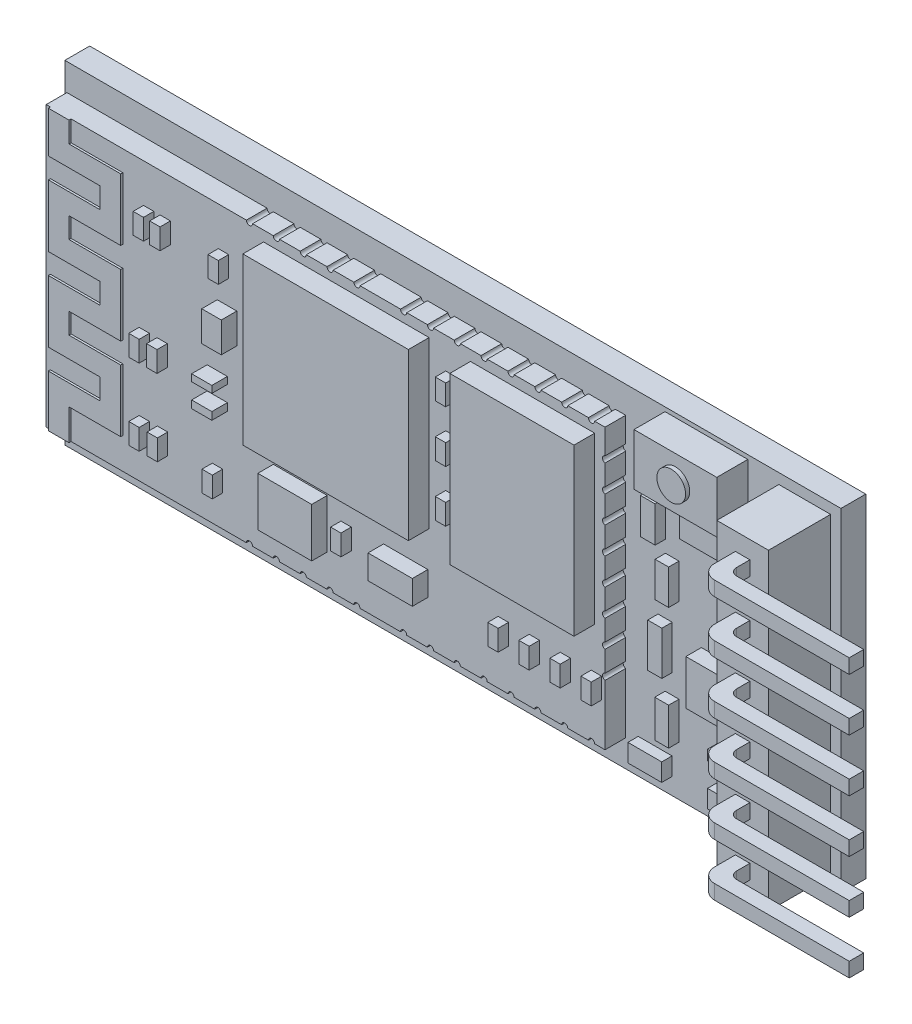
SolidWorks part; units mm, degrees
ref_plane "Ön Düzlem" through (0, 0, 0) normal (0, 0, 1) x (1, 0, 0)
ref_plane "Üst Düzlem" through (0, 0, 0) normal (0, 1, 0) x (1, 0, 0)
ref_plane "Sağ Düzlem" through (0, 0, 0) normal (1, 0, 0) x (0, 0, -1)
sketch "Çizim2" plane through (0, 0, 0) normal (0, 0, 1) x (1, 0, 0)
  line L1 (0, 0) -> (37.5, 0)
  line L2 (0, 0) -> (0, 16.1)
  line L3 (0, 16.1) -> (37.5, 16.1)
  line L4 (37.5, 0) -> (37.5, 16.1)
  dimension "D1" = 37.5
  dimension "D2" = 16.1
extrude "Yükseklik-Ekstrüzyon1" add sketch "Çizim2" along normal blind 1.2
sketch "Çizim5" plane through (0, 0, 1.2) normal (0, 0, 1) x (1, 0, 0)
  line L0 (37.5, 0) -> (37.5, 16.1) construction
  line L1 (34.5, 0.5) -> (37, 0.5)
  line L2 (34.5, 0.5) -> (34.5, 15.6)
  line L3 (34.5, 15.6) -> (37, 15.6)
  line L4 (37, 0.5) -> (37, 15.6)
  line L5 (0, 0) -> (37.5, 0) construction
  line L6 (37.5, 16.1) -> (0, 16.1) construction
  dimension "D1" = 0.5
  dimension "D2" = 0.5
  dimension "D3" = 0.5
  dimension "D4" = 2.5
extrude "Yükseklik-Ekstrüzyon2" add sketch "Çizim5" along normal blind 3
sketch "Çizim14" plane through (0, 0, 1.2) normal (0, 0, 1) x (1, 0, 0)
  line L1 (0.1, 14.8) -> (27.1, 14.8)
  line L2 (0.1, 14.8) -> (0.1, 1.3)
  line L3 (0.1, 1.3) -> (27.1, 1.3)
  line L4 (27.1, 14.8) -> (27.1, 1.3)
  line L5 (37.5, 16.1) -> (0, 16.1) construction
  line L7 (0, 16.1) -> (0, 0) construction
  point P6 (0, 8.05)
  dimension "D1" = 13.5
  dimension "D2" = 27
  dimension "D3" = 1.3
  dimension "D4" = 0.1
extrude "Yükseklik-Ekstrüzyon10" add sketch "Çizim14" along normal blind 1
sketch "Çizim15" plane through (0, 0, 2.2) normal (0, 0, 1) x (1, 0, 0)
  line L0 (0.3, 1.3) -> (0.3, 14.8) construction
  line L1 (0.1, 1.3) -> (27.1, 1.3) construction
  line L2 (27.1, 14.8) -> (0.1, 14.8) construction
  line L3 (0.1, 14.8) -> (0.1, 1.3) construction
  line L4 (3.8, 14.8) -> (3.8, 1.3) construction
  line L5 (0.3, 1.3) -> (0.3, 3.8)
  line L6 (1.3, 2.8) -> (3.8, 2.8)
  line L7 (3.8, 2.8) -> (3.8, 5.8)
  line L8 (0.3, 3.8) -> (2.8, 3.8)
  line L9 (1.3, 1.3) -> (1.3, 2.8)
  line L10 (0.1, 1.3) -> (27.1, 1.3) construction
  line L11 (2.8, 3.8) -> (2.8, 4.8)
  line L12 (2.8, 4.8) -> (0.3, 4.8)
  line L13 (0.3, 4.8) -> (0.3, 7.8)
  line L14 (0.3, 7.8) -> (2.8, 7.8)
  line L15 (3.8, 5.8) -> (1.3, 5.8)
  line L16 (1.3, 5.8) -> (1.3, 6.8)
  line L17 (1.3, 6.8) -> (3.8, 6.8)
  line L18 (3.8, 6.8) -> (3.8, 9.8)
  line L19 (2.8, 7.8) -> (2.8, 8.8)
  line L20 (2.8, 8.8) -> (0.3, 8.8)
  line L21 (0.3, 8.8) -> (0.3, 11.8)
  line L22 (3.8, 9.8) -> (1.3, 9.8)
  line L23 (1.3, 9.8) -> (1.3, 10.8)
  line L24 (1.3, 10.8) -> (3.8, 10.8)
  line L25 (3.8, 10.8) -> (3.8, 13.8)
  line L26 (0.3, 11.8) -> (2.8, 11.8)
  line L27 (2.8, 11.8) -> (2.8, 12.8)
  line L28 (2.8, 12.8) -> (0.3, 12.8)
  line L29 (0.3, 12.8) -> (0.3, 14.8)
  line L30 (3.8, 13.8) -> (1.3, 13.8)
  line L31 (1.3, 13.8) -> (1.3, 14.8)
  line L32 (1.3, 14.8) -> (0.3, 14.8)
  line L33 (1.3, 1.3) -> (0.3, 1.3)
  dimension "D1" = 0.2
  dimension "D2" = 3.5
  dimension "D3" = 2.5
  dimension "D4" = 1
  dimension "D5" = 1.5
  dimension "D6" = 3
  dimension "D7" = 1
  dimension "D8" = 1
  dimension "D9" = 1
  dimension "D10" = 1
  dimension "D11" = 1
  dimension "D12" = 2.5
  dimension "D13" = 3
  dimension "D14" = 2.5
  dimension "D15" = 3
  dimension "D16" = 1
  dimension "D17" = 1
  dimension "D18" = 1
  dimension "D19" = 2.5
  dimension "D20" = 2.5
  dimension "D21" = 1
  dimension "D22" = 3
  dimension "D23" = 1
extrude "Yükseklik-Ekstrüzyon11" add sketch "Çizim15" along normal blind 0.1
sketch "Çizim16" plane through (0, 0, 1.2) normal (0, 0, 1) x (1, 0, 0)
  line L0 (37.5, 16.1) -> (0, 16.1) construction
  line L1 (29, 15.9) -> (33, 15.9)
  line L2 (29, 15.9) -> (29, 13.4)
  line L3 (29, 13.4) -> (33, 13.4)
  line L4 (33, 15.9) -> (33, 13.4)
  line L5 (34.5, 15.6) -> (34.5, 0.5) construction
  dimension "D1" = 2.5
  dimension "D2" = 4
  dimension "D3" = 0.2
  dimension "D4" = 1.5
extrude "Yükseklik-Ekstrüzyon12" add sketch "Çizim16" along normal blind 1.5 separate body
sketch "Çizim17" plane through (0, 0, 2.7) normal (0, 0, 1) x (1, 0, 0)
  line L0 (29, 14.65) -> (33, 14.65) construction
  line L1 (29, 15.9) -> (29, 13.4) construction
  line L2 (33, 13.4) -> (33, 15.9) construction
  line L3 (31, 15.9) -> (31, 13.4) construction
  line L4 (33, 15.9) -> (29, 15.9) construction
  line L5 (29, 13.4) -> (33, 13.4) construction
  circle A0 centre (31, 14.65) radius 0.6936
extrude "Yükseklik-Ekstrüzyon13" add sketch "Çizim17" along normal blind 0.2
sketch "Çizim18" plane through (0, 0, 2.2) normal (0, 0, 1) x (1, 0, 0)
  line L0 (27.1, 14.8) -> (1.3, 14.8) construction
  line L1 (26.6004, 6.3) -> (20.6004, 6.3)
  line L2 (26.6004, 6.3) -> (26.6004, 14.3)
  line L3 (26.6004, 14.3) -> (20.6004, 14.3)
  line L4 (20.6004, 6.3) -> (20.6004, 14.3)
  line L5 (27.1, 1.3) -> (27.1, 14.8) construction
  line L7 (18.6004, 6.3) -> (10.6004, 6.3)
  line L8 (18.6004, 6.3) -> (18.6004, 14.3)
  line L9 (18.6004, 14.3) -> (10.6004, 14.3)
  line L10 (10.6004, 6.3) -> (10.6004, 14.3)
  dimension "D1" = 8
  dimension "D2" = 6
  dimension "D3" = 0.5
  dimension "D4" = 0.4996
  dimension "D5" = 2
  dimension "D6" = 8
  dimension "D7" = 8
  dimension "D8" = 0.5
extrude "Yükseklik-Ekstrüzyon14" add sketch "Çizim18" along normal blind 1
sketch "Çizim19" plane through (0, 0, 2.2) normal (0, 0, 1) x (1, 0, 0)
  line L0 (3.8, 10.8) -> (3.8, 13.8) construction
  line L1 (4.8, 11.93) -> (5.3, 11.93)
  line L2 (4.8, 11.93) -> (4.8, 12.93)
  line L3 (4.8, 12.93) -> (5.3, 12.93)
  line L4 (5.3, 11.93) -> (5.3, 12.93)
  line L5 (5.6, 11.93) -> (6.1, 11.93)
  line L6 (5.6, 11.93) -> (5.6, 12.93)
  line L7 (5.6, 12.93) -> (6.1, 12.93)
  line L8 (6.1, 11.93) -> (6.1, 12.93)
  line L9 (8.4157, 11.93) -> (8.9157, 11.93)
  line L10 (8.4157, 11.93) -> (8.4157, 12.93)
  line L11 (8.4157, 12.93) -> (8.9157, 12.93)
  line L12 (8.9157, 11.93) -> (8.9157, 12.93)
  dimension "D1" = 1
  dimension "D2" = 0.5
  dimension "D3" = 1
  dimension "D4" = 0.5
  dimension "D5" = 1
  dimension "D6" = 0.5
  dimension "D7" = 1
  dimension "D8" = 0.3
extrude "Yükseklik-Ekstrüzyon15" add sketch "Çizim19" along normal blind 0.5
sketch "Çizim22" plane through (0, 0, 2.2) normal (0, 0, 1) x (1, 0, 0)
  line L0 (4.589, 6.722) -> (5.089, 6.722)
  line L1 (4.589, 6.722) -> (4.589, 7.722)
  line L2 (4.589, 7.722) -> (5.089, 7.722)
  line L3 (5.089, 6.722) -> (5.089, 7.722)
  line L4 (5.4516, 6.722) -> (5.9516, 6.722)
  line L5 (5.4516, 6.722) -> (5.4516, 7.722)
  line L6 (5.4516, 7.722) -> (5.9516, 7.722)
  line L7 (5.9516, 6.722) -> (5.9516, 7.722)
  line L8 (4.5888, 3.0335) -> (5.0888, 3.0335)
  line L9 (4.5888, 3.0335) -> (4.5888, 4.0335)
  line L10 (4.5888, 4.0335) -> (5.0888, 4.0335)
  line L11 (5.0888, 3.0335) -> (5.0888, 4.0335)
  line L12 (5.4701, 3.0335) -> (5.9701, 3.0335)
  line L13 (5.4701, 3.0335) -> (5.4701, 4.0335)
  line L14 (5.4701, 4.0335) -> (5.9701, 4.0335)
  line L15 (5.9701, 3.0335) -> (5.9701, 4.0335)
  line L16 (8.1243, 2.8062) -> (8.6243, 2.8062)
  line L17 (8.1243, 2.8062) -> (8.1243, 3.8062)
  line L18 (8.1243, 3.8062) -> (8.6243, 3.8062)
  line L19 (8.6243, 2.8062) -> (8.6243, 3.8062)
  line L20 (19.4004, 12.3) -> (19.9004, 12.3)
  line L21 (19.4004, 12.3) -> (19.4004, 13.3)
  line L22 (19.4004, 13.3) -> (19.9004, 13.3)
  line L23 (19.9004, 12.3) -> (19.9004, 13.3)
  line L24 (19.4004, 9.8) -> (19.9004, 9.8)
  line L25 (19.4004, 9.8) -> (19.4004, 10.8)
  line L26 (19.4004, 10.8) -> (19.9004, 10.8)
  line L27 (19.9004, 9.8) -> (19.9004, 10.8)
  line L28 (19.9004, 7.3) -> (19.4004, 7.3)
  line L29 (19.9004, 7.3) -> (19.9004, 8.3)
  line L30 (19.9004, 8.3) -> (19.4004, 8.3)
  line L31 (19.4004, 7.3) -> (19.4004, 8.3)
  line L32 (26.4351, 3.3) -> (26.9351, 3.3)
  line L33 (26.4351, 3.3) -> (26.4351, 4.3)
  line L34 (26.4351, 4.3) -> (26.9351, 4.3)
  line L35 (26.9351, 3.3) -> (26.9351, 4.3)
  line L36 (24.9351, 3.3) -> (25.4351, 3.3)
  line L37 (24.9351, 3.3) -> (24.9351, 4.3)
  line L38 (24.9351, 4.3) -> (25.4351, 4.3)
  line L39 (25.4351, 3.3) -> (25.4351, 4.3)
  line L40 (23.4351, 3.3) -> (23.9351, 3.3)
  line L41 (23.4351, 3.3) -> (23.4351, 4.3)
  line L42 (23.4351, 4.3) -> (23.9351, 4.3)
  line L43 (23.9351, 3.3) -> (23.9351, 4.3)
  line L44 (21.9351, 3.3) -> (22.4351, 3.3)
  line L45 (21.9351, 3.3) -> (21.9351, 4.3)
  line L46 (21.9351, 4.3) -> (22.4351, 4.3)
  line L47 (22.4351, 3.3) -> (22.4351, 4.3)
  line L48 (14.3404, 3.4908) -> (14.8404, 3.4908)
  line L49 (14.3404, 3.4908) -> (14.3404, 4.4908)
  line L50 (14.3404, 4.4908) -> (14.8404, 4.4908)
  line L51 (14.8404, 3.4908) -> (14.8404, 4.4908)
  line L52 (27.1, 14.8) -> (1.3, 14.8) construction
  line L54 (20.6004, 14.3) -> (20.6004, 6.3) construction
  line L55 (20.6004, 6.3) -> (26.6004, 6.3) construction
  dimension "D1" = 1
  dimension "D2" = 1
  dimension "D3" = 1
  dimension "D4" = 1
  dimension "D5" = 1
  dimension "D6" = 1
  dimension "D7" = 1
  dimension "D8" = 1
  dimension "D9" = 1
  dimension "D10" = 1
  dimension "D11" = 1
  dimension "D12" = 1
  dimension "D13" = 1
  dimension "D14" = 0.5
  dimension "D15" = 0.5
  dimension "D16" = 0.5
  dimension "D17" = 1.5
  dimension "D18" = 1.5
  dimension "D19" = 1.5
  dimension "D20" = 0.7
  dimension "D21" = 2
  dimension "D22" = 1
  dimension "D23" = 1
  dimension "D24" = 1
  dimension "D25" = 0.5
  dimension "D26" = 0.5
  dimension "D27" = 0.5
  dimension "D28" = 0.5
extrude "Yükseklik-Ekstrüzyon17" add sketch "Çizim22" along normal blind 0.5
sketch "Çizim23" plane through (0, 0, 2.2) normal (0, 0, 1) x (1, 0, 0)
  line L1 (11.0751, 2.8642) -> (13.6775, 2.8642)
  line L2 (11.0751, 2.8642) -> (11.0751, 5.2317)
  line L3 (11.0751, 5.2317) -> (13.6775, 5.2317)
  line L4 (13.6775, 2.8642) -> (13.6775, 5.2317)
  line L6 (16.3989, 3.3962) -> (18.5402, 3.3962)
  line L7 (16.3989, 3.3962) -> (16.3989, 4.5627)
  line L8 (16.3989, 4.5627) -> (18.5402, 4.5627)
  line L9 (18.5402, 3.3962) -> (18.5402, 4.5627)
  line L10 (7.8761, 6.3372) -> (8.8522, 6.3372)
  line L11 (7.8761, 6.3372) -> (7.8761, 6.7031)
  line L12 (7.8761, 6.7031) -> (8.8522, 6.7031)
  line L13 (8.8522, 6.3372) -> (8.8522, 6.7031)
  line L14 (7.8761, 7.4637) -> (8.8522, 7.4637)
  line L15 (7.8761, 7.4637) -> (7.8761, 7.7984)
  line L16 (7.8761, 7.7984) -> (8.8522, 7.7984)
  line L17 (8.8522, 7.4637) -> (8.8522, 7.7984)
  line L18 (8.3641, 9.3029) -> (9.3075, 9.3029)
  line L19 (8.3641, 9.3029) -> (8.3641, 10.7632)
  line L20 (8.3641, 10.7632) -> (9.3075, 10.7632)
  line L21 (9.3075, 9.3029) -> (9.3075, 10.7632)
extrude "Yükseklik-Ekstrüzyon18" add sketch "Çizim23" along normal blind 0.75
sketch "Çizim24" plane through (0, 0, 1.2) normal (0, 0, 1) x (1, 0, 0)
  line L1 (30.2001, 11.4276) -> (32.9069, 11.4276)
  line L2 (30.2001, 11.4276) -> (30.2001, 13.1705)
  line L3 (30.2001, 13.1705) -> (32.9069, 13.1705)
  line L4 (32.9069, 11.4276) -> (32.9069, 13.1705)
  line L5 (28.3044, 10.5724) -> (29.0208, 10.5724)
  line L6 (28.3044, 10.5724) -> (28.3044, 12.2991)
  line L7 (28.3044, 12.2991) -> (29.0208, 12.2991)
  line L8 (29.0208, 10.5724) -> (29.0208, 12.2991)
  line L9 (29.0208, 8.2903) -> (29.6736, 8.2903)
  line L10 (29.0208, 8.2903) -> (29.0208, 9.9841)
  line L11 (29.0208, 9.9841) -> (29.6736, 9.9841)
  line L12 (29.6736, 8.2903) -> (29.6736, 9.9841)
  line L13 (28.6626, 5.1548) -> (29.3472, 5.1548)
  line L14 (28.6626, 5.1548) -> (28.6626, 7.2612)
  line L15 (28.6626, 7.2612) -> (29.3472, 7.2612)
  line L16 (29.3472, 5.1548) -> (29.3472, 7.2612)
  line L17 (29.0049, 2.403) -> (29.6736, 2.403)
  line L18 (29.0049, 2.403) -> (29.0049, 4.2038)
  line L19 (29.0049, 4.2038) -> (29.6736, 4.2038)
  line L20 (29.6736, 2.403) -> (29.6736, 4.2038)
  line L21 (27.7053, 0.8007) -> (29.3393, 0.8007)
  line L22 (27.7053, 0.8007) -> (27.7053, 1.6631)
  line L23 (27.7053, 1.6631) -> (29.3393, 1.6631)
  line L24 (29.3393, 0.8007) -> (29.3393, 1.6631)
  line L25 (31.5535, 0.8007) -> (32.9069, 0.8007)
  line L26 (31.5535, 0.8007) -> (31.5535, 1.6631)
  line L27 (31.5535, 1.6631) -> (32.9069, 1.6631)
  line L28 (32.9069, 0.8007) -> (32.9069, 1.6631)
  line L29 (31.5535, 2.804) -> (32.9069, 2.804)
  line L30 (31.5535, 2.804) -> (31.5535, 3.3034)
  line L31 (31.5535, 3.3034) -> (32.9069, 3.3034)
  line L32 (32.9069, 2.804) -> (32.9069, 3.3034)
  line L33 (32.0202, 10.8077) -> (33.3885, 10.8077)
  line L34 (32.0202, 10.8077) -> (32.0202, 9.9841)
  line L35 (32.0202, 9.9841) -> (33.3885, 9.9841)
  line L36 (33.3885, 10.8077) -> (33.3885, 9.9841)
  line L37 (32.0202, 8.2903) -> (33.3885, 8.2903)
  line L38 (32.0202, 8.2903) -> (32.0202, 9.082)
  line L39 (32.0202, 9.082) -> (33.3885, 9.082)
  line L40 (33.3885, 8.2903) -> (33.3885, 9.082)
extrude "Yükseklik-Ekstrüzyon19" add sketch "Çizim24" along normal blind 0.5
sketch "Çizim25" plane through (0, 0, 1.2) normal (0, 0, 1) x (1, 0, 0)
  line L1 (30.7569, 4.7405) -> (33.8081, 4.7405)
  line L2 (30.7569, 4.7405) -> (30.7569, 6.9062)
  line L3 (30.7569, 6.9062) -> (33.8081, 6.9062)
  line L4 (33.8081, 4.7405) -> (33.8081, 6.9062)
extrude "Yükseklik-Ekstrüzyon20" add sketch "Çizim25" along normal blind 0.75
sketch "Çizim27" plane through (0, 0, 2.2) normal (0, 0, 1) x (1, 0, 0)
  line L0 (27.1, 14.8) -> (1.3, 14.8) construction
  line L1 (27.1, 1.3) -> (27.1, 14.8) construction
  line L2 (26.6, 14.8) -> (26.3, 14.8)
  line L3 (25.3, 14.8) -> (25.0045, 14.8)
  line L4 (24.5045, 14.4582) -> (24.5045, 15.2412) construction
  line L5 (23.7089, 14.8) -> (24.0045, 14.8)
  line L6 (22.4089, 14.8) -> (22.7089, 14.8)
  line L7 (21.9089, 14.5317) -> (21.9089, 15.1738) construction
  line L8 (21.4089, 14.8) -> (21.1089, 14.8)
  line L9 (20.1089, 14.8) -> (19.8134, 14.8)
  line L10 (18.5179, 14.8) -> (18.8134, 14.8)
  line L11 (17.2179, 14.8) -> (17.5179, 14.8)
  line L12 (16.2399, 14.5317) -> (16.2399, 15.1738) construction
  line L13 (10.5708, 14.5317) -> (10.5708, 15.1738) construction
  line L14 (15.2619, 14.8) -> (14.9619, 14.8)
  line L15 (13.9619, 14.8) -> (13.6663, 14.8)
  line L16 (12.3708, 14.8) -> (12.6663, 14.8)
  line L17 (11.0708, 14.8) -> (11.3708, 14.8)
  line L18 (10.0708, 14.8) -> (9.7708, 14.8)
  line L19 (27.1, 8.05) -> (0.1, 8.05) construction
  line L20 (0.1, 14.8) -> (0.1, 1.3) construction
  line L21 (10.5708, 1.5683) -> (10.5708, 0.9262) construction
  line L22 (16.2399, 1.5683) -> (16.2399, 0.9262) construction
  line L23 (21.9089, 1.5683) -> (21.9089, 0.9262) construction
  line L24 (24.5045, 1.6418) -> (24.5045, 0.8588) construction
  line L25 (10.0708, 1.3) -> (9.7708, 1.3)
  line L26 (11.0708, 1.3) -> (11.3708, 1.3)
  line L27 (12.3708, 1.3) -> (12.6663, 1.3)
  line L28 (13.9619, 1.3) -> (13.6663, 1.3)
  line L29 (15.2619, 1.3) -> (14.9619, 1.3)
  line L30 (17.2179, 1.3) -> (17.5179, 1.3)
  line L31 (18.5179, 1.3) -> (18.8134, 1.3)
  line L32 (20.1089, 1.3) -> (19.8134, 1.3)
  line L33 (21.4089, 1.3) -> (21.1089, 1.3)
  line L34 (22.4089, 1.3) -> (22.7089, 1.3)
  line L35 (23.7089, 1.3) -> (24.0045, 1.3)
  line L36 (25.3, 1.3) -> (25.0045, 1.3)
  line L37 (26.6, 1.3) -> (26.3, 1.3)
  arc A0 (26.6, 14.8) -> (26.3, 14.8) centre (26.45, 14.8) cw
  arc A1 (25.3, 14.8) -> (25.0045, 14.8) centre (25.1522, 14.8) cw
  arc A2 (23.7089, 14.8) -> (24.0045, 14.8) centre (23.8567, 14.8) ccw
  arc A3 (22.4089, 14.8) -> (22.7089, 14.8) centre (22.5589, 14.8) ccw
  arc A4 (21.4089, 14.8) -> (21.1089, 14.8) centre (21.2589, 14.8) cw
  arc A5 (20.1089, 14.8) -> (19.8134, 14.8) centre (19.9612, 14.8) cw
  arc A6 (18.5179, 14.8) -> (18.8134, 14.8) centre (18.6656, 14.8) ccw
  arc A7 (17.2179, 14.8) -> (17.5179, 14.8) centre (17.3679, 14.8) ccw
  arc A8 (15.2619, 14.8) -> (14.9619, 14.8) centre (15.1119, 14.8) cw
  arc A9 (13.9619, 14.8) -> (13.6663, 14.8) centre (13.8141, 14.8) cw
  arc A10 (12.3708, 14.8) -> (12.6663, 14.8) centre (12.5186, 14.8) ccw
  arc A11 (11.0708, 14.8) -> (11.3708, 14.8) centre (11.2208, 14.8) ccw
  arc A12 (10.0708, 14.8) -> (9.7708, 14.8) centre (9.9208, 14.8) cw
  arc A13 (10.0708, 1.3) -> (9.7708, 1.3) centre (9.9208, 1.3) ccw
  arc A14 (11.0708, 1.3) -> (11.3708, 1.3) centre (11.2208, 1.3) cw
  arc A15 (12.3708, 1.3) -> (12.6663, 1.3) centre (12.5186, 1.3) cw
  arc A16 (13.9619, 1.3) -> (13.6663, 1.3) centre (13.8141, 1.3) ccw
  arc A17 (15.2619, 1.3) -> (14.9619, 1.3) centre (15.1119, 1.3) ccw
  arc A18 (17.2179, 1.3) -> (17.5179, 1.3) centre (17.3679, 1.3) cw
  arc A19 (18.5179, 1.3) -> (18.8134, 1.3) centre (18.6656, 1.3) cw
  arc A20 (20.1089, 1.3) -> (19.8134, 1.3) centre (19.9612, 1.3) ccw
  arc A21 (21.4089, 1.3) -> (21.1089, 1.3) centre (21.2589, 1.3) ccw
  arc A22 (22.4089, 1.3) -> (22.7089, 1.3) centre (22.5589, 1.3) cw
  arc A23 (23.7089, 1.3) -> (24.0045, 1.3) centre (23.8567, 1.3) cw
  arc A24 (25.3, 1.3) -> (25.0045, 1.3) centre (25.1522, 1.3) ccw
  arc A25 (26.6, 1.3) -> (26.3, 1.3) centre (26.45, 1.3) ccw
  dimension "D1" = 0.5
  dimension "D2" = 0.3
  dimension "D3" = 1
  dimension "D4" = 0.5
  dimension "D5" = 0.5
extrude "Kes-Ekstrüzyon1" cut sketch "Çizim27" against normal blind 1
sketch "Çizim28" plane through (0, 0, 2.2) normal (0, 0, 1) x (1, 0, 0)
  line L0 (27.1, 1.3) -> (27.1, 14.8) construction
  line L1 (27.1, 13.3005) -> (27.1, 13.5998)
  line L2 (26.7694, 12.8005) -> (27.3012, 12.8005) construction
  line L3 (27.1, 12.3005) -> (27.1, 12.0011)
  line L4 (26.8075, 11.5011) -> (27.3621, 11.5011) construction
  line L5 (27.1, 10.7018) -> (27.1, 11.0011)
  line L6 (27.1, 9.7018) -> (27.1, 9.4024)
  line L7 (26.7694, 8.9024) -> (27.3621, 8.9024) construction
  line L8 (27.3621, 8.9024) -> (27.0657, 8.9024) construction
  line L9 (26.8075, 6.3037) -> (27.3621, 6.3037) construction
  line L10 (26.7694, 5.0044) -> (27.3012, 5.0044) construction
  line L11 (27.1, 8.1031) -> (27.1, 8.4024)
  line L12 (27.1, 7.1031) -> (27.1, 6.8037)
  line L13 (27.1, 5.5044) -> (27.1, 5.8037)
  line L14 (27.1, 4.5044) -> (27.1, 4.205)
  arc A0 (27.1, 13.5998) -> (27.1, 13.3005) centre (27.1317, 13.4502) ccw
  arc A1 (27.1, 12.0011) -> (27.1, 12.3005) centre (27.1317, 12.1508) cw
  arc A2 (27.1, 11.0011) -> (27.1, 10.7018) centre (27.1317, 10.8514) ccw
  arc A3 (27.1, 9.4024) -> (27.1, 9.7018) centre (27.1317, 9.5521) cw
  arc A4 (27.1, 8.4024) -> (27.1, 8.1031) centre (27.1317, 8.2527) ccw
  arc A5 (27.1, 6.8037) -> (27.1, 7.1031) centre (27.1317, 6.9534) cw
  arc A6 (27.1, 5.8037) -> (27.1, 5.5044) centre (27.1317, 5.654) ccw
  arc A7 (27.1, 4.205) -> (27.1, 4.5044) centre (27.1317, 4.3547) cw
  dimension "D1" = 0.5
  dimension "D2" = 0.5
  dimension "D3" = 0.5
extrude "Kes-Ekstrüzyon2" cut sketch "Çizim28" against normal blind 1
sketch "Sketch1" plane through (0, 0, 4.2) normal (0, 0, 1) x (1, 0, 0)
  line L0 (34.5, 0.5) -> (37, 0.5) construction
  line L1 (35.4, 1.35) -> (36.1, 1.35)
  line L2 (35.4, 1.35) -> (35.4, 2.05)
  line L3 (35.4, 2.05) -> (36.1, 2.05)
  line L4 (36.1, 1.35) -> (36.1, 2.05)
  line L5 (35.4, 1.35) -> (36.1, 2.05) construction
  line L6 (35.4, 2.05) -> (36.1, 1.35) construction
  line L7 (35.4, 3.89) -> (35.4, 4.59)
  line L8 (35.4, 3.89) -> (36.1, 3.89)
  line L9 (36.1, 3.89) -> (36.1, 4.59)
  line L10 (35.4, 4.59) -> (36.1, 4.59)
  line L11 (35.4, 6.43) -> (35.4, 7.13)
  line L12 (35.4, 6.43) -> (36.1, 6.43)
  line L13 (36.1, 6.43) -> (36.1, 7.13)
  line L14 (35.4, 7.13) -> (36.1, 7.13)
  line L15 (35.4, 8.97) -> (35.4, 9.67)
  line L16 (35.4, 8.97) -> (36.1, 8.97)
  line L17 (36.1, 8.97) -> (36.1, 9.67)
  line L18 (35.4, 9.67) -> (36.1, 9.67)
  line L19 (35.4, 11.51) -> (35.4, 12.21)
  line L20 (35.4, 11.51) -> (36.1, 11.51)
  line L21 (36.1, 11.51) -> (36.1, 12.21)
  line L22 (35.4, 12.21) -> (36.1, 12.21)
  line L23 (35.4, 14.05) -> (35.4, 14.75)
  line L24 (35.4, 14.05) -> (36.1, 14.05)
  line L25 (36.1, 14.05) -> (36.1, 14.75)
  line L26 (35.4, 14.75) -> (36.1, 14.75)
  line L27 (35.75, 7.13) -> (35.75, 8.97) construction
  line L28 (37, 0.5) -> (37, 15.6) construction
  point P0 (35.75, 1.7)
  point P8 (35.75, 0.5)
  point P32 (37, 8.05)
  point P33 (35.75, 8.05)
  dimension "D1" = 0.7
  dimension "D3" = 2.54
  dimension "D2" = 6
extrude "Boss-Extrude1" add sketch "Sketch1" along normal blind 1.7
sketch "Sketch2" plane through (36.1, 0, 0) normal (1, 0, 0) x (0, 0, -1)
  line L0 (-5.9, 2.05) -> (-4.2, 2.05) construction
  line L1 (-5.9, 1.35) -> (-5.2, 1.35)
  line L2 (-5.9, 1.35) -> (-5.9, 2.05)
  line L3 (-5.9, 2.05) -> (-5.2, 2.05)
  line L4 (-5.2, 1.35) -> (-5.2, 2.05)
  line L5 (-5.9, 3.89) -> (-5.9, 4.59)
  line L6 (-5.9, 3.89) -> (-5.2, 3.89)
  line L7 (-5.2, 3.89) -> (-5.2, 4.59)
  line L8 (-5.9, 4.59) -> (-5.2, 4.59)
  line L9 (-5.9, 6.43) -> (-5.9, 7.13)
  line L10 (-5.9, 6.43) -> (-5.2, 6.43)
  line L11 (-5.2, 6.43) -> (-5.2, 7.13)
  line L12 (-5.9, 7.13) -> (-5.2, 7.13)
  line L13 (-5.9, 8.97) -> (-5.9, 9.67)
  line L14 (-5.9, 8.97) -> (-5.2, 8.97)
  line L15 (-5.2, 8.97) -> (-5.2, 9.67)
  line L16 (-5.9, 9.67) -> (-5.2, 9.67)
  line L17 (-5.9, 11.51) -> (-5.9, 12.21)
  line L18 (-5.9, 11.51) -> (-5.2, 11.51)
  line L19 (-5.2, 11.51) -> (-5.2, 12.21)
  line L20 (-5.9, 12.21) -> (-5.2, 12.21)
  line L21 (-5.9, 14.05) -> (-5.9, 14.75)
  line L22 (-5.9, 14.05) -> (-5.2, 14.05)
  line L23 (-5.2, 14.05) -> (-5.2, 14.75)
  line L24 (-5.9, 14.75) -> (-5.2, 14.75)
  dimension "D1" = 6
extrude "Boss-Extrude2" add sketch "Sketch2" along normal blind 6.5
fillet "Fillet1" radius 0.7 6 edges at (35.4, 11.86, 5.9) (35.4, 14.4, 5.9) (35.4, 9.32, 5.9) (35.4, 4.24, 5.9) (35.4, 6.78, 5.9) (35.4, 1.7, 5.9)
fillet "Fillet2" radius 0.35 6 edges at (36.1, 14.4, 5.2) (36.1, 11.86, 5.2) (36.1, 9.32, 5.2) (36.1, 6.78, 5.2) (36.1, 1.7, 5.2) (36.1, 4.24, 5.2)
